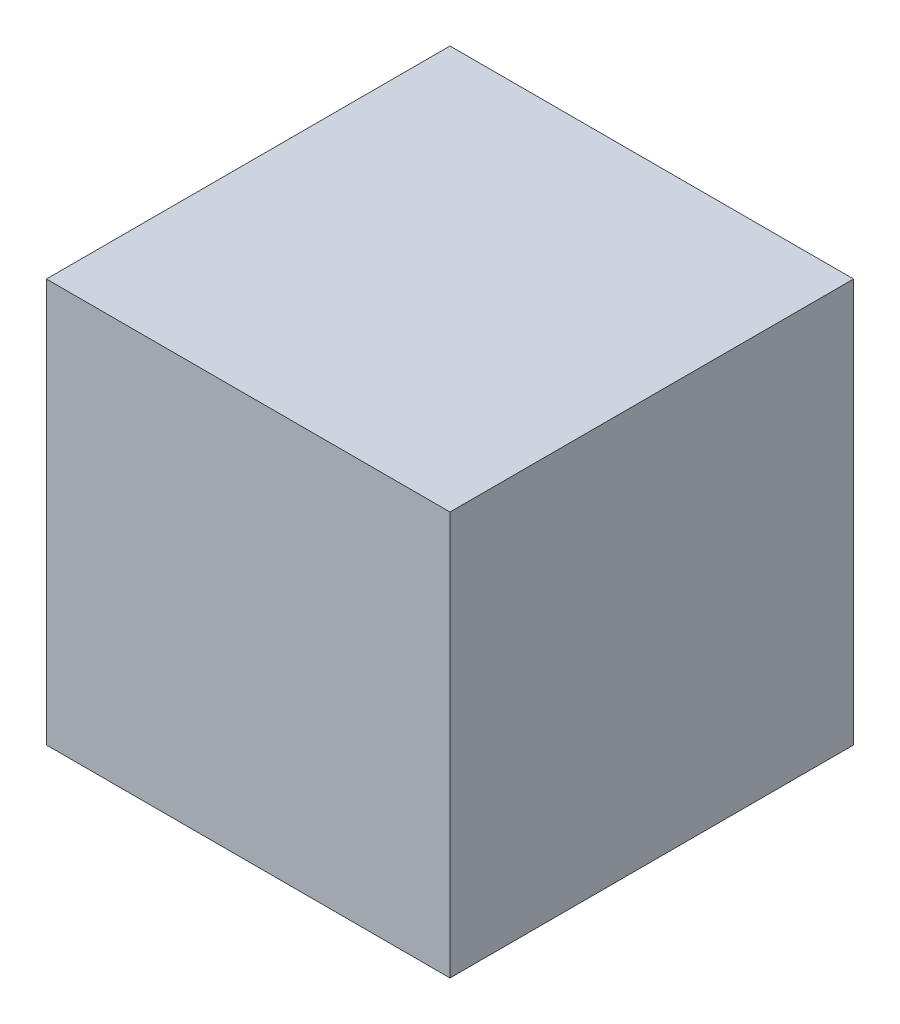
SolidWorks part; units mm, degrees
ref_plane "Front Plane" through (0, 0, 0) normal (0, 0, 1) x (1, 0, 0)
ref_plane "Top Plane" through (0, 0, 0) normal (0, 1, 0) x (1, 0, 0)
ref_plane "Right Plane" through (0, 0, 0) normal (1, 0, 0) x (0, 0, -1)
sketch "Sketch1" plane through (0, 0, 0) normal (0, 1, 0) x (1, 0, 0)
  line L0 (-24.8221, -25.0552) -> (-24.8221, 432.1448)
  line L1 (-24.8221, 432.1448) -> (432.3779, 432.1448)
  line L2 (-24.8221, 432.1448) -> (-24.8221, -25.0552)
  line L3 (-24.8221, -25.0552) -> (432.3779, -25.0552)
  line L4 (432.3779, 432.1448) -> (432.3779, -25.0552)
  line L5 (-24.8221, -25.0552) -> (432.3779, -25.0552)
extrude "Boss-Extrude1" add sketch "Sketch1" along normal blind 457.2 contours L4 L1 L0 L3
